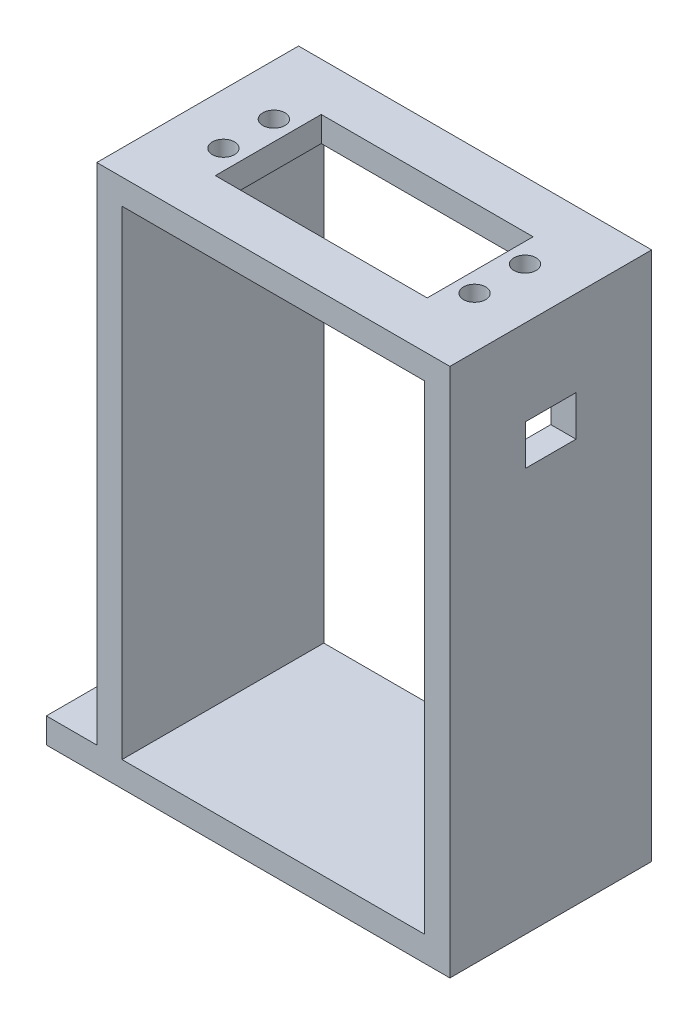
SolidWorks part; units mm, degrees
ref_plane "Front Plane" through (0, 0, 0) normal (0, 0, 1) x (1, 0, 0)
ref_plane "Top Plane" through (0, 0, 0) normal (0, 1, 0) x (1, 0, 0)
ref_plane "Right Plane" through (0, 0, 0) normal (1, 0, 0) x (0, 0, -1)
sketch "Sketch2" plane through (0, 0, 0) normal (0, 1, 0) x (1, 0, 0)
  line L1 (0, 0) -> (-80, 0)
  line L2 (0, 0) -> (0, 40)
  line L3 (0, 40) -> (-80, 40)
  line L4 (-80, 0) -> (-80, 40)
  circle A0 centre (-75, 25) radius 2.2
  circle A1 centre (-75, 15) radius 2.2
  dimension "D3" = 4.4
  dimension "D4" = 4.4
  dimension "D1" = 40
  dimension "D2" = 80
  dimension "D5" = 10
  dimension "D6" = 15
  dimension "D7" = 5
extrude "Boss-Extrude1" add sketch "Sketch2" along normal blind 5
sketch "Sketch3" plane through (0, 5, 0) normal (0, 1, 0) x (1, 0, 0)
  line L0 (-70, 0) -> (-70, 40)
  line L1 (-65, 0) -> (-65, 40)
  line L2 (-5, 0) -> (-5, 40)
  line L4 (0, 0) -> (0, 40)
  line L5 (0, 40) -> (-80, 40)
  line L6 (-80, 40) -> (-80, 0)
  line L7 (-80, 0) -> (0, 0)
  line L8 (0, 0) -> (0, 40)
  line L9 (0, 40) -> (-80, 40)
  line L10 (-80, 40) -> (-80, 0)
  line L11 (-80, 0) -> (0, 0)
  line M9 (0, 0) -> (0, 40)
  line M10 (0, 40) -> (-80, 40)
  line M12 (-80, 0) -> (0, 0)
  dimension "D2" = 70
  dimension "D3" = 5
  dimension "D4" = 5
  dimension "D1" = 0
extrude "Boss-Extrude2" add sketch "Sketch3" along normal blind 100 contours L2 M12 M9 M10 | L1 L0 M12 M10
sketch "Sketch4" plane through (0, 0, 0) normal (1, 0, 0) x (0, 0, -1)
  line L1 (15, 88) -> (25, 88)
  line L2 (15, 88) -> (15, 80)
  line L3 (15, 80) -> (25, 80)
  line L4 (0, 0) -> (40, 0)
  line L5 (40, 0) -> (40, 105)
  line L6 (40, 105) -> (0, 105)
  line L7 (0, 105) -> (0, 0)
  line L8 (0, 0) -> (40, 0)
  line L9 (40, 0) -> (40, 105)
  line L10 (40, 105) -> (0, 105)
  line L11 (0, 105) -> (0, 0)
  line L12 (25, 88) -> (25, 80)
  dimension "D2" = 17
  dimension "D3" = 25
  dimension "D4" = 10
  dimension "D5" = 15
  dimension "D6" = 15
  dimension "D1" = 0
extrude "Cut-Extrude1" cut sketch "Sketch4" against normal blind 10 contours L12 L1 L2 L3
sketch "Sketch5" plane through (0, 0, 0) normal (1, 0, 0) x (0, 0, -1)
  line L0 (0, 100) -> (40, 100)
  line L4 (0, 0) -> (40, 0)
  line L5 (40, 0) -> (40, 105)
  line L6 (40, 105) -> (0, 105)
  line L7 (0, 105) -> (0, 0)
  line L8 (0, 0) -> (40, 0)
  line L9 (40, 0) -> (40, 105)
  line L10 (40, 105) -> (0, 105)
  line L11 (0, 105) -> (0, 0)
  line M7 (40, 0) -> (40, 105)
  line M8 (40, 105) -> (0, 105)
  line M9 (0, 105) -> (0, 0)
  dimension "D2" = 5
  dimension "D1" = 0
extrude "Boss-Extrude3" add sketch "Sketch5" against normal blind 70 contours L0 M9 M7 M8
sketch "Sketch6" plane through (0, 105, 0) normal (0, 1, 0) x (1, 0, 0)
  line L0 (-70, 0) -> (-70, 40) construction
  line L1 (-14, 9.5) -> (-56, 9.5)
  line L2 (-14, 9.5) -> (-14, 30.5)
  line L3 (-14, 30.5) -> (-56, 30.5)
  line L4 (-56, 9.5) -> (-56, 30.5)
  line L5 (-70, 0) -> (0, 0) construction
  line L6 (0, 40) -> (-70, 40) construction
  line L7 (-56, 20) -> (-70, 20) construction
  line L8 (-35, 30.5) -> (-35, 9.5) construction
  circle A0 centre (-59.89, 25) radius 2.2
  circle A1 centre (-59.89, 15) radius 2.2
  circle A2 centre (-10.11, 15) radius 2.2
  circle A3 centre (-10.11, 25) radius 2.2
  dimension "D6" = 4.4
  dimension "D7" = 4.4
  dimension "D1" = 42
  dimension "D2" = 21
  dimension "D3" = 14
  dimension "D4" = 9.5
  dimension "D5" = 9.5
  dimension "D8" = 3.89
  dimension "D9" = 10
  dimension "D10" = 5
extrude "Cut-Extrude2" cut sketch "Sketch6" against normal blind 70
sketch "Sketch7" plane through (0, 0, 0) normal (0, -1, 0) x (1, 0, 0)
  circle A0 centre (-75, -25) radius 2.2 construction
  circle A1 centre (-75, -15) radius 2.2 construction
  circle A2 centre (-75, -25) radius 2.2
  circle A3 centre (-75, -15) radius 2.2
  circle A4 centre (-75, -15) radius 4
  circle A5 centre (-75, -25) radius 4
  dimension "D1" = 8
  dimension "D2" = 8
extrude "Cut-Extrude3" cut sketch "Sketch7" against normal blind 3
